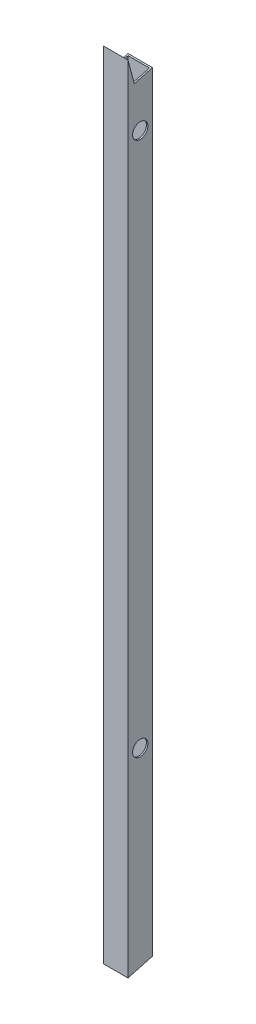
SolidWorks part; units mm, degrees
ref_plane "Front Plane" through (0, 0, 0) normal (0, 0, 1) x (1, 0, 0)
ref_plane "Top Plane" through (0, 0, 0) normal (0, 1, 0) x (1, 0, 0)
ref_plane "Right Plane" through (0, 0, 0) normal (1, 0, 0) x (0, 0, -1)
sketch "Sketch1" plane through (0, 0, 0) normal (0, 1, 0) x (1, 0, 0)
  line L1 (-59.3551, 50.3766) -> (-33.9551, 50.3766)
  line L2 (-59.3551, 50.3766) -> (-59.3551, 24.9766)
  line L3 (-59.3551, 24.9766) -> (-33.9551, 24.9766)
  line L4 (-33.9551, 50.3766) -> (-33.9551, 24.9766)
  line L5 (-57.8311, 48.8526) -> (-35.4791, 48.8526)
  line L6 (-57.8311, 48.8526) -> (-57.8311, 26.5006)
  line L7 (-57.8311, 26.5006) -> (-35.4791, 26.5006)
  line L8 (-35.4791, 48.8526) -> (-35.4791, 26.5006)
  dimension "D1" = 25.4
  dimension "D2" = 25.4
  dimension "D3" = 1.524
  dimension "D4" = 1.524
  dimension "D5" = 1.524
  dimension "D6" = 1.524
extrude "Boss-Extrude1" add sketch "Sketch1" along normal blind 883.666
sketch "Sketch5" plane through (-33.9551, 0, 0) normal (1, 0, 0) x (0, 0, -1)
  line L0 (50.3766, 883.666) -> (50.3766, 0) construction
  line L1 (24.9766, 0) -> (50.3766, 0) construction
  circle A0 centre (37.6766, 258.318) radius 7.9375
  dimension "D1" = 15.875
  dimension "D2" = 12.7
  dimension "D3" = 258.318
extrude "Cut-Extrude3" cut sketch "Sketch5" against normal through all both and the other way through all
sketch "Sketch6" plane through (-33.9551, 0, 0) normal (1, 0, 0) x (0, 0, -1)
  line L1 (50.3766, 883.666) -> (50.3766, 0) construction
  circle A1 centre (37.6766, 813.943) radius 7.9375
  dimension "D2" = 15.875
  dimension "D5" = 12.7
extrude "Cut-Extrude4" cut sketch "Sketch6" against normal through all both and the other way through all
sketch "Sketch7" plane through (-33.9551, 0, 0) normal (1, 0, 0) x (0, 0, -1)
  line L1 (24.9766, 883.666) -> (31.5284, 859.2143)
  line L7 (50.3766, 883.666) -> (24.9766, 883.666)
  line L8 (31.5284, 859.2143) -> (50.3766, 864.2646)
  line L9 (50.3766, 864.2646) -> (50.3766, 883.666)
  line L10 (50.3766, 883.666) -> (50.3766, 0) construction
  dimension "D1" = 75
  dimension "D2" = 90
extrude "Cut-Extrude5" cut sketch "Sketch7" against normal through all both and the other way through all
sketch "Sketch8" plane through (-33.9551, 0, 0) normal (1, 0, 0) x (0, 0, -1)
  line L1 (24.9766, 883.666) -> (24.9766, 0) construction
  line L2 (24.9766, 57.658) -> (24.9766, 0)
  line L3 (24.9766, 0) -> (50.3766, 0)
  line L5 (50.3766, 864.2646) -> (50.3766, 0) construction
  line L6 (50.3766, 64.516) -> (50.3766, 0)
  line L7 (24.9766, 57.658) -> (50.3766, 64.516)
  dimension "D1" = 64.516
  dimension "D2" = 57.658
extrude "Cut-Extrude6" cut sketch "Sketch8" against normal through all both and the other way through all
